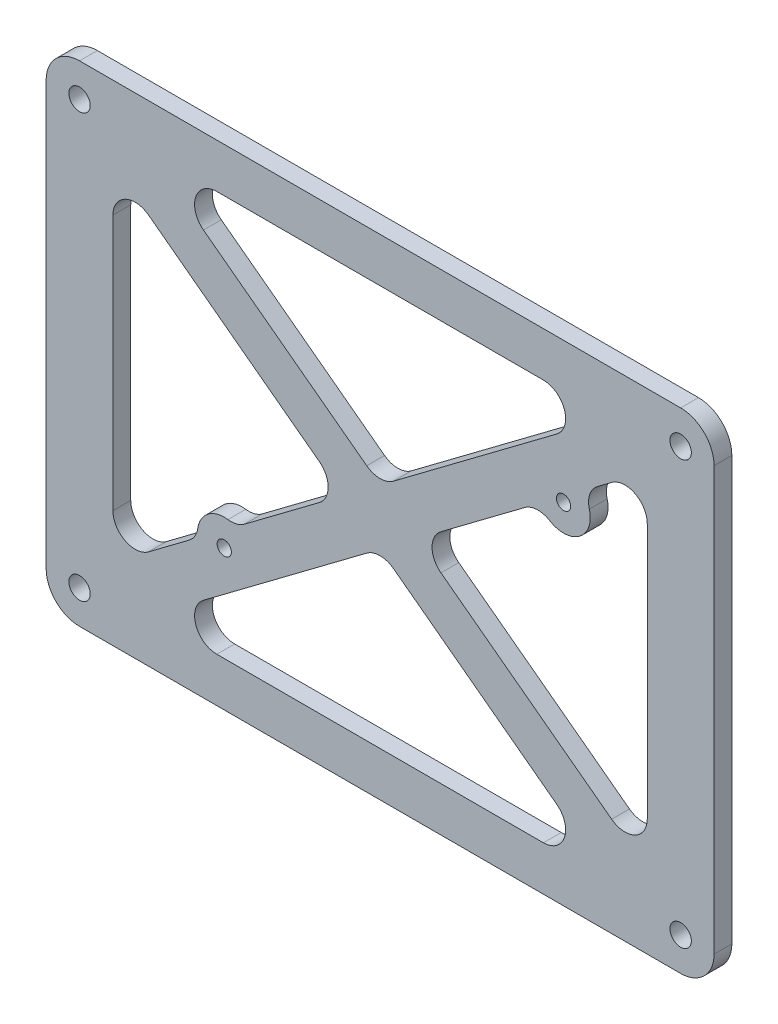
SolidWorks part; units mm, degrees
ref_plane "正面" through (0, 0, 0) normal (1, 0, 0) x (0, 1, 0)
ref_plane "平面" through (0, 0, 0) normal (0, 0, 1) x (0, 1, 0)
ref_plane "右側面" through (0, 0, 0) normal (0, 1, 0) x (-1, 0, 0)
sketch "ｽｹｯﾁ1" plane through (0, 0, 0) normal (0, 0, 1) x (0, 1, 0)
  line L1 (0, 0) -> (110, 0)
  line L2 (0, 0) -> (0, 150)
  line L3 (0, 150) -> (110, 150)
  line L4 (110, 0) -> (110, 150)
  line L5 (0, 0) -> (110, 150) construction
  line L6 (0, 150) -> (110, 0) construction
  point P4 (55, 75)
  dimension "D1" = 110
  dimension "D2" = 150
extrude "ﾎﾞｽ - 押し出し1" add sketch "ｽｹｯﾁ1" along normal blind 4
sketch "ｽｹｯﾁ2" plane through (0, 0, 4) normal (0, 0, 1) x (1, 0, 0)
  line L0 (-150, 110) -> (-150, 0) construction
  line L1 (0, 0) -> (0, 110) construction
  line L2 (0, 110) -> (-150, 110) construction
  line L3 (-150, 0) -> (0, 0) construction
  point P0 (-142.5, 102.5)
  point P1 (-142.5, 7.5)
  point P2 (-7.5, 102.5)
  point P3 (-7.5, 7.5)
  point P8 (0, 0)
  point P9 (0, 0)
  point P14 (0, 0)
  point P15 (0, 0)
  point P16 (-245.8927, 86.7037)
  point P17 (0, 0)
  dimension "D1" = 7.5
  dimension "D2" = 7.5
  dimension "D3" = 7.5
  dimension "D4" = 7.5
hole_wizard "M4 すきま穴1" positions "ｽｹｯﾁ2" profile "ｽｹｯﾁ3" hole size "M4" standard "JIS" end condition through all
sketch "ｽｹｯﾁ3" plane through (-142.5, 102.5, 4) normal (1, 0, 0) x (0, -1, 0)
  line L0 (0, 0) -> (0, 4)
  line L1 (0, 4) -> (2.4, 4)
  line L2 (2.4, 4) -> (2.4, 0)
  line L5 (2.4, 0) -> (0, 0)
  line L11 (0, -6.35) -> (0, 107.95) construction
  dimension "通し穴の直径" = 4.8
  dimension "通し穴の深さ" = 4
sketch "ｽｹｯﾁ4" plane through (0, 0, 4) normal (0, 0, 1) x (1, 0, 0)
  line L0 (-150, 110) -> (-150, 0) construction
  line L1 (-150, 0) -> (0, 0) construction
  point P0 (-110, 31.5)
  point P1 (-33.8, 78.49)
  point P6 (-185.7233, 120.3705)
  dimension "D1" = 40
  dimension "D2" = 76.2
  dimension "D3" = 46.99
  dimension "D4" = 31.5
hole_wizard "M3 すきま穴1" positions "ｽｹｯﾁ4" profile "ｽｹｯﾁ5" hole size "M3" standard "JIS" end condition through all
sketch "ｽｹｯﾁ5" plane through (-110, 31.5, 4) normal (1, 0, 0) x (0, -1, 0)
  line L0 (0, 0) -> (0, 4)
  line L1 (0, 4) -> (1.6, 4)
  line L2 (1.6, 4) -> (1.6, 0)
  line L5 (1.6, 0) -> (0, 0)
  line L11 (0, -6.35) -> (0, 107.95) construction
  dimension "通し穴の直径" = 3.2
  dimension "通し穴の深さ" = 4
sketch "ｽｹｯﾁ6" plane through (0, 0, 4) normal (0, 0, 1) x (1, 0, 0)
  line L0 (0, 110) -> (-150, 110) construction
  line L1 (-126.6667, 10) -> (-23.3333, 10)
  line L2 (-135, 16.25) -> (-135, 93.75)
  line L3 (-126.6667, 100) -> (-23.3333, 100)
  line L4 (-15, 16.25) -> (-15, 93.75)
  line L5 (-135, 10) -> (-15, 100) construction
  line L6 (-135, 100) -> (-15, 10) construction
  line L7 (-150, 110) -> (-150, 0) construction
  line L9 (-150, 0) -> (0, 0) construction
  line L10 (-126.6667, 10) -> (-75, 48.75)
  line L11 (-135, 16.25) -> (-115.9253, 30.556)
  line L12 (-135, 93.75) -> (-83.3333, 55)
  line L13 (-126.6667, 100) -> (-75, 61.25)
  line L14 (-29.6146, 82.7891) -> (-15, 93.75)
  line L15 (-132, 104) -> (-12, 14) construction
  line L16 (-138, 96) -> (-18, 6) construction
  line L17 (-132, 6) -> (-12, 96) construction
  line L18 (-138, 14) -> (-18, 104) construction
  line L19 (-39.099, 75.6757) -> (-29.6146, 82.7891) construction
  line L20 (-107.4347, 36.924) -> (-83.3333, 55)
  line L21 (-115.9253, 30.556) -> (-107.4347, 36.924) construction
  line L22 (-75, 48.75) -> (-23.3333, 10)
  line L23 (-79.1667, 51.875) -> (-75, 48.75) construction
  line L24 (-83.3333, 55) -> (-79.1667, 51.875) construction
  line L25 (-75, 61.25) -> (-23.3333, 100)
  line L26 (-83.3333, 55) -> (-79.1667, 58.125) construction
  line L27 (-79.1667, 58.125) -> (-75, 61.25) construction
  line L28 (-66.6667, 55) -> (-15, 16.25)
  line L29 (-75, 61.25) -> (-70.8333, 58.125) construction
  line L30 (-70.8333, 58.125) -> (-66.6667, 55) construction
  line L31 (-66.6667, 55) -> (-39.099, 75.6757)
  line L32 (-70.8333, 51.875) -> (-66.6667, 55) construction
  line L33 (-75, 48.75) -> (-70.8333, 51.875) construction
  line L34 (-135, 100) -> (-126.6667, 100) construction
  line L35 (-135, 93.75) -> (-135, 100) construction
  line L36 (-23.3333, 100) -> (-15, 100) construction
  line L37 (-15, 93.75) -> (-15, 100) construction
  line L38 (-15, 10) -> (-15, 16.25) construction
  line L39 (-23.3333, 10) -> (-15, 10) construction
  line L40 (-135, 10) -> (-126.6667, 10) construction
  line L41 (-135, 10) -> (-135, 16.25) construction
  line L42 (0, 0) -> (0, 110) construction
  line L43 (0, 110) -> (-150, 110)
  line L44 (0, 0) -> (0, 110)
  line L45 (-150, 0) -> (0, 0)
  line L46 (-150, 110) -> (-150, 0)
  arc A0 (-107.4347, 36.924) -> (-115.9253, 30.556) centre (-110, 31.5) ccw
  arc A1 (-39.099, 75.6757) -> (-29.6146, 82.7891) centre (-33.8, 78.49) ccw
  arc A2 (-29.6146, 82.7891) -> (-36.6154, 83.7884) centre (-33.8, 78.49) ccw construction
  arc A3 (-36.6154, 83.7884) -> (-38.0982, 82.6764) centre (-33.8, 78.49) ccw construction
  arc A4 (-38.0982, 82.6764) -> (-39.099, 75.6757) centre (-33.8, 78.49) ccw construction
  arc A5 (-113.9811, 27.011) -> (-107.4347, 36.924) centre (-110, 31.5) ccw construction
  arc A6 (-114.2553, 27.27) -> (-113.9811, 27.011) centre (-110, 31.5) ccw construction
  arc A7 (-115.9253, 30.556) -> (-114.2553, 27.27) centre (-110, 31.5) ccw construction
  point P6 (-75, 55)
  point P13 (-75, 110)
  point P14 (0, 0)
  point P15 (-115, 31.5)
  point P16 (-150, 55)
  point P18 (-115.7378, 30.6967)
  point P50 (-114.3276, 31.5)
  point P51 (-114.3333, 31.5)
  point P52 (0, 0)
  point P53 (-116.9236, 30.6944)
  point P54 (0, 0)
  point P55 (-117.142, 30.8544)
  point P56 (-120, 30.6361)
  point P57 (0, 0)
  point P58 (-120, 31.5)
  dimension "D1" = 12
  dimension "D2" = 12
  dimension "D3" = 15
  dimension "D4" = 10
  dimension "D5" = 5
  dimension "5" = 5
  dimension "D7" = 5
  dimension "D8" = 5
extrude "ｶｯﾄ - 押し出し1" cut sketch "ｽｹｯﾁ6" against normal through all flip side to cut
fillet "ﾌｨﾚｯﾄ3" radius 5 16 edges at (-126.6667, 100, 2) (-75, 61.25, 2) (-23.3333, 100, 2) (-15, 93.75, 2) (-66.6667, 55, 2) (-15, 16.25, 2) (-23.3333, 10, 2) (-126.6667, 10, 2) (-75, 48.75, 2) (-83.3333, 55, 2) (-135, 93.75, 2) (-135, 16.25, 2) (-107.4347, 36.924, 2) (-115.9253, 30.556, 2) (-39.099, 75.6757, 2) (-29.6146, 82.7891, 2)
fillet "ﾌｨﾚｯﾄ1" radius 7.5 4 edges at (0, 110, 2) (-150, 110, 2) (-150, 0, 2) (0, 0, 2)
